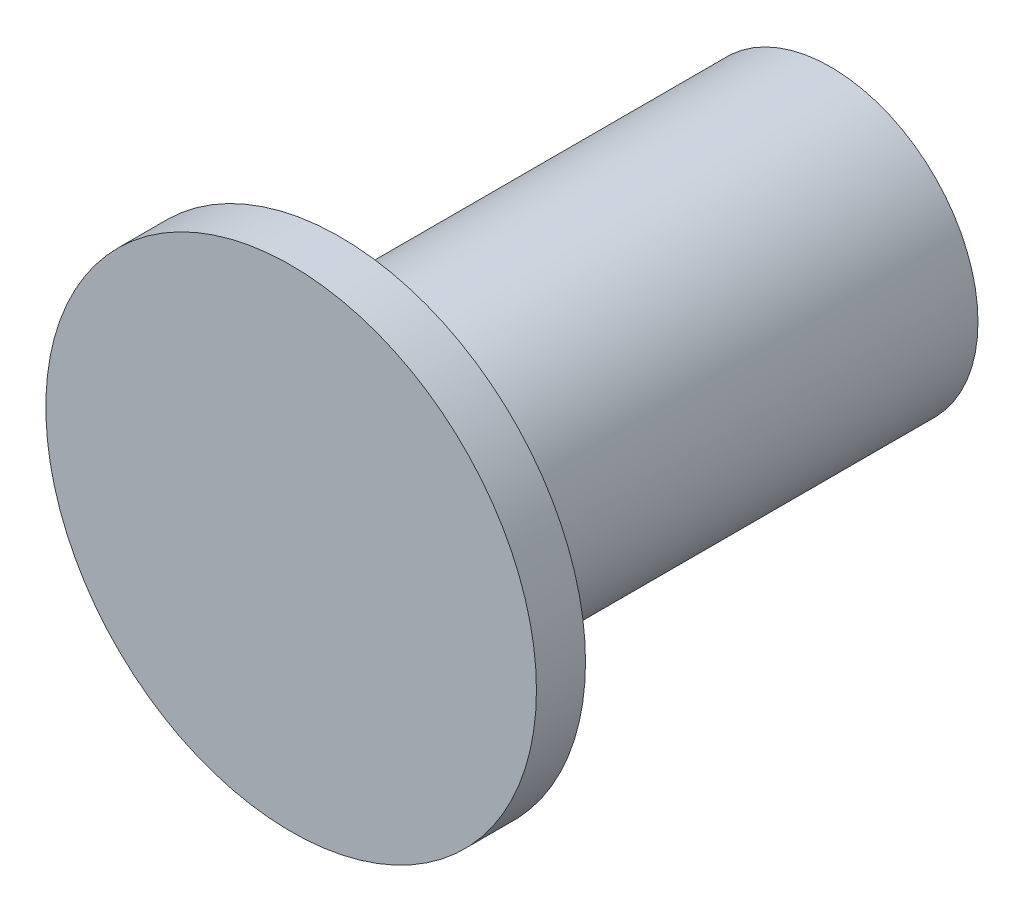
SolidWorks part; units mm, degrees
ref_plane "前视基准面" through (0, 0, 0) normal (0, 0, 1) x (1, 0, 0)
ref_plane "上视基准面" through (0, 0, 0) normal (0, 1, 0) x (1, 0, 0)
ref_plane "右视基准面" through (0, 0, 0) normal (1, 0, 0) x (0, 0, -1)
sketch "草图1" plane through (0, 0, 0) normal (0, 0, 1) x (1, 0, 0)
  circle A0 centre (0, 0) radius 0.3
extrude "凸台-拉伸1" add sketch "草图1" along normal blind 1
sketch "草图2" plane through (0, 0, 1) normal (0, 0, 1) x (1, 0, 0)
  circle A0 centre (0, 0) radius 0.5
extrude "凸台-拉伸2" add sketch "草图2" along normal blind 0.1
